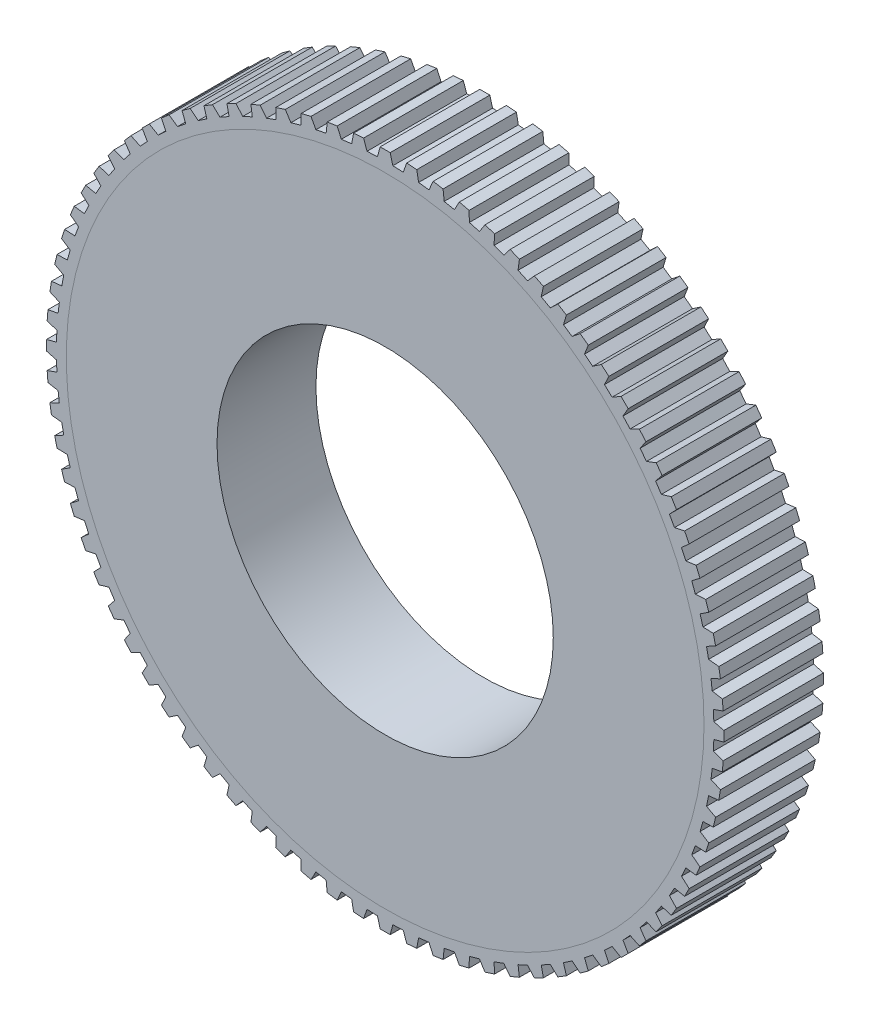
SolidWorks part; units mm, degrees
ref_plane "Front Plane" through (0, 0, 0) normal (0, 0, 1) x (1, 0, 0)
ref_plane "Top Plane" through (0, 0, 0) normal (0, 1, 0) x (1, 0, 0)
ref_plane "Right Plane" through (0, 0, 0) normal (1, 0, 0) x (0, 0, -1)
sketch "Sketch1" plane through (0, 0, 0) normal (0, 0, 1) x (1, 0, 0)
  circle A0 centre (0, 0) radius 8.5
  circle A1 centre (0, 0) radius 16.12
  dimension "D1" = 17
  dimension "D2" = 7.62
extrude "Boss-Extrude1" add sketch "Sketch1" along normal mid plane 5
sketch "Sketch2" plane through (0, 0, 0) normal (0, 0, 1) x (1, 0, 0)
  line L0 (0, 0) -> (0, 17.12) construction
  line L1 (-0.254, 17.12) -> (0.254, 17.12)
  line L2 (-0.254, 17.12) -> (-0.3892, 16.6154)
  line L3 (0.254, 17.12) -> (0.3892, 16.6154)
  line L4 (1.09, 17.0872) -> (0.9156, 16.5948)
  line L5 (1.09, 17.0872) -> (1.5964, 17.0473)
  line L6 (1.5964, 17.0473) -> (1.6916, 16.5337)
  line L7 (2.4273, 16.949) -> (2.2148, 16.4718)
  line L8 (2.4273, 16.949) -> (2.929, 16.8695)
  line L9 (2.929, 16.8695) -> (2.9836, 16.35)
  line L10 (3.7496, 16.7063) -> (3.5004, 16.2472)
  line L11 (3.7496, 16.7063) -> (4.2436, 16.5877)
  line L12 (4.2436, 16.5877) -> (4.2572, 16.0655)
  line L13 (5.0488, 16.3606) -> (4.7643, 15.9225)
  line L14 (5.0488, 16.3606) -> (5.5319, 16.2036)
  line L15 (5.5319, 16.2036) -> (5.5046, 15.682)
  line L16 (6.3169, 15.914) -> (5.9989, 15.4996)
  line L17 (6.3169, 15.914) -> (6.7862, 15.7196)
  line L18 (6.7862, 15.7196) -> (6.718, 15.2017)
  line L19 (7.546, 15.3693) -> (7.1965, 14.9812)
  line L20 (7.546, 15.3693) -> (7.9986, 15.1387)
  line L21 (7.9986, 15.1387) -> (7.89, 14.6278)
  line L22 (8.7286, 14.7299) -> (8.3497, 14.3703)
  line L23 (8.7286, 14.7299) -> (9.1617, 14.4645)
  line L24 (9.1617, 14.4645) -> (9.0134, 13.9636)
  line L25 (9.8574, 13.9997) -> (9.4514, 13.6709)
  line L26 (9.8574, 13.9997) -> (10.2684, 13.7011)
  line L27 (10.2684, 13.7011) -> (10.0812, 13.2134)
  line L28 (10.9254, 13.1831) -> (10.4949, 12.8872)
  line L29 (10.9254, 13.1831) -> (11.3117, 12.8532)
  line L30 (11.3117, 12.8532) -> (11.0868, 12.3817)
  line L31 (11.9261, 12.2853) -> (11.4737, 12.0241)
  line L32 (11.9261, 12.2853) -> (12.2853, 11.9261)
  line L33 (12.2853, 11.9261) -> (12.0241, 11.4737)
  line L34 (12.8532, 11.3117) -> (12.3817, 11.0868)
  line L35 (12.8532, 11.3117) -> (13.1831, 10.9254)
  line L36 (13.1831, 10.9254) -> (12.8872, 10.4949)
  line L37 (13.7011, 10.2684) -> (13.2134, 10.0812)
  line L38 (13.7011, 10.2684) -> (13.9997, 9.8574)
  line L39 (13.9997, 9.8574) -> (13.6709, 9.4514)
  line L40 (14.4645, 9.1617) -> (13.9636, 9.0134)
  line L41 (14.4645, 9.1617) -> (14.7299, 8.7286)
  line L42 (14.7299, 8.7286) -> (14.3703, 8.3497)
  line L43 (15.1387, 7.9986) -> (14.6278, 7.89)
  line L44 (15.1387, 7.9986) -> (15.3693, 7.546)
  line L45 (15.3693, 7.546) -> (14.9812, 7.1965)
  line L46 (15.7196, 6.7862) -> (15.2017, 6.718)
  line L47 (15.7196, 6.7862) -> (15.914, 6.3169)
  line L48 (15.914, 6.3169) -> (15.4996, 5.9989)
  line L49 (16.2036, 5.5319) -> (15.682, 5.5046)
  line L50 (16.2036, 5.5319) -> (16.3606, 5.0488)
  line L51 (16.3606, 5.0488) -> (15.9225, 4.7643)
  line L52 (16.5877, 4.2436) -> (16.0655, 4.2572)
  line L53 (16.5877, 4.2436) -> (16.7063, 3.7496)
  line L54 (16.7063, 3.7496) -> (16.2472, 3.5004)
  line L55 (16.8695, 2.929) -> (16.35, 2.9836)
  line L56 (16.8695, 2.929) -> (16.949, 2.4273)
  line L57 (16.949, 2.4273) -> (16.4718, 2.2148)
  line L58 (17.0473, 1.5964) -> (16.5337, 1.6916)
  line L59 (17.0473, 1.5964) -> (17.0872, 1.09)
  line L60 (17.0872, 1.09) -> (16.5948, 0.9156)
  line L61 (17.12, 0.254) -> (16.6154, 0.3892)
  line L62 (17.12, 0.254) -> (17.12, -0.254)
  line L63 (17.12, -0.254) -> (16.6154, -0.3892)
  line L64 (17.0872, -1.09) -> (16.5948, -0.9156)
  line L65 (17.0872, -1.09) -> (17.0473, -1.5964)
  line L66 (17.0473, -1.5964) -> (16.5337, -1.6916)
  line L67 (16.949, -2.4273) -> (16.4718, -2.2148)
  line L68 (16.949, -2.4273) -> (16.8695, -2.929)
  line L69 (16.8695, -2.929) -> (16.35, -2.9836)
  line L70 (16.7063, -3.7496) -> (16.2472, -3.5004)
  line L71 (16.7063, -3.7496) -> (16.5877, -4.2436)
  line L72 (16.5877, -4.2436) -> (16.0655, -4.2572)
  line L73 (16.3606, -5.0488) -> (15.9225, -4.7643)
  line L74 (16.3606, -5.0488) -> (16.2036, -5.5319)
  line L75 (16.2036, -5.5319) -> (15.682, -5.5046)
  line L76 (15.914, -6.3169) -> (15.4996, -5.9989)
  line L77 (15.914, -6.3169) -> (15.7196, -6.7862)
  line L78 (15.7196, -6.7862) -> (15.2017, -6.718)
  line L79 (15.3693, -7.546) -> (14.9812, -7.1965)
  line L80 (15.3693, -7.546) -> (15.1387, -7.9986)
  line L81 (15.1387, -7.9986) -> (14.6278, -7.89)
  line L82 (14.7299, -8.7286) -> (14.3703, -8.3497)
  line L83 (14.7299, -8.7286) -> (14.4645, -9.1617)
  line L84 (14.4645, -9.1617) -> (13.9636, -9.0134)
  line L85 (13.9997, -9.8574) -> (13.6709, -9.4514)
  line L86 (13.9997, -9.8574) -> (13.7011, -10.2684)
  line L87 (13.7011, -10.2684) -> (13.2134, -10.0812)
  line L88 (13.1831, -10.9254) -> (12.8872, -10.4949)
  line L89 (13.1831, -10.9254) -> (12.8532, -11.3117)
  line L90 (12.8532, -11.3117) -> (12.3817, -11.0868)
  line L91 (12.2853, -11.9261) -> (12.0241, -11.4737)
  line L92 (12.2853, -11.9261) -> (11.9261, -12.2853)
  line L93 (11.9261, -12.2853) -> (11.4737, -12.0241)
  line L94 (11.3117, -12.8532) -> (11.0868, -12.3817)
  line L95 (11.3117, -12.8532) -> (10.9254, -13.1831)
  line L96 (10.9254, -13.1831) -> (10.4949, -12.8872)
  line L97 (10.2684, -13.7011) -> (10.0812, -13.2134)
  line L98 (10.2684, -13.7011) -> (9.8574, -13.9997)
  line L99 (9.8574, -13.9997) -> (9.4514, -13.6709)
  line L100 (9.1617, -14.4645) -> (9.0134, -13.9636)
  line L101 (9.1617, -14.4645) -> (8.7286, -14.7299)
  line L102 (8.7286, -14.7299) -> (8.3497, -14.3703)
  line L103 (7.9986, -15.1387) -> (7.89, -14.6278)
  line L104 (7.9986, -15.1387) -> (7.546, -15.3693)
  line L105 (7.546, -15.3693) -> (7.1965, -14.9812)
  line L106 (6.7862, -15.7196) -> (6.718, -15.2017)
  line L107 (6.7862, -15.7196) -> (6.3169, -15.914)
  line L108 (6.3169, -15.914) -> (5.9989, -15.4996)
  line L109 (5.5319, -16.2036) -> (5.5046, -15.682)
  line L110 (5.5319, -16.2036) -> (5.0488, -16.3606)
  line L111 (5.0488, -16.3606) -> (4.7643, -15.9225)
  line L112 (4.2436, -16.5877) -> (4.2572, -16.0655)
  line L113 (4.2436, -16.5877) -> (3.7496, -16.7063)
  line L114 (3.7496, -16.7063) -> (3.5004, -16.2472)
  line L115 (2.929, -16.8695) -> (2.9836, -16.35)
  line L116 (2.929, -16.8695) -> (2.4273, -16.949)
  line L117 (2.4273, -16.949) -> (2.2148, -16.4718)
  line L118 (1.5964, -17.0473) -> (1.6916, -16.5337)
  line L119 (1.5964, -17.0473) -> (1.09, -17.0872)
  line L120 (1.09, -17.0872) -> (0.9156, -16.5948)
  line L121 (0.254, -17.12) -> (0.3892, -16.6154)
  line L122 (0.254, -17.12) -> (-0.254, -17.12)
  line L123 (-0.254, -17.12) -> (-0.3892, -16.6154)
  line L124 (-1.09, -17.0872) -> (-0.9156, -16.5948)
  line L125 (-1.09, -17.0872) -> (-1.5964, -17.0473)
  line L126 (-1.5964, -17.0473) -> (-1.6916, -16.5337)
  line L127 (-2.4273, -16.949) -> (-2.2148, -16.4718)
  line L128 (-2.4273, -16.949) -> (-2.929, -16.8695)
  line L129 (-2.929, -16.8695) -> (-2.9836, -16.35)
  line L130 (-3.7496, -16.7063) -> (-3.5004, -16.2472)
  line L131 (-3.7496, -16.7063) -> (-4.2436, -16.5877)
  line L132 (-4.2436, -16.5877) -> (-4.2572, -16.0655)
  line L133 (-5.0488, -16.3606) -> (-4.7643, -15.9225)
  line L134 (-5.0488, -16.3606) -> (-5.5319, -16.2036)
  line L135 (-5.5319, -16.2036) -> (-5.5046, -15.682)
  line L136 (-6.3169, -15.914) -> (-5.9989, -15.4996)
  line L137 (-6.3169, -15.914) -> (-6.7862, -15.7196)
  line L138 (-6.7862, -15.7196) -> (-6.718, -15.2017)
  line L139 (-7.546, -15.3693) -> (-7.1965, -14.9812)
  line L140 (-7.546, -15.3693) -> (-7.9986, -15.1387)
  line L141 (-7.9986, -15.1387) -> (-7.89, -14.6278)
  line L142 (-8.7286, -14.7299) -> (-8.3497, -14.3703)
  line L143 (-8.7286, -14.7299) -> (-9.1617, -14.4645)
  line L144 (-9.1617, -14.4645) -> (-9.0134, -13.9636)
  line L145 (-9.8574, -13.9997) -> (-9.4514, -13.6709)
  line L146 (-9.8574, -13.9997) -> (-10.2684, -13.7011)
  line L147 (-10.2684, -13.7011) -> (-10.0812, -13.2134)
  line L148 (-10.9254, -13.1831) -> (-10.4949, -12.8872)
  line L149 (-10.9254, -13.1831) -> (-11.3117, -12.8532)
  line L150 (-11.3117, -12.8532) -> (-11.0868, -12.3817)
  line L151 (-11.9261, -12.2853) -> (-11.4737, -12.0241)
  line L152 (-11.9261, -12.2853) -> (-12.2853, -11.9261)
  line L153 (-12.2853, -11.9261) -> (-12.0241, -11.4737)
  line L154 (-12.8532, -11.3117) -> (-12.3817, -11.0868)
  line L155 (-12.8532, -11.3117) -> (-13.1831, -10.9254)
  line L156 (-13.1831, -10.9254) -> (-12.8872, -10.4949)
  line L157 (-13.7011, -10.2684) -> (-13.2134, -10.0812)
  line L158 (-13.7011, -10.2684) -> (-13.9997, -9.8574)
  line L159 (-13.9997, -9.8574) -> (-13.6709, -9.4514)
  line L160 (-14.4645, -9.1617) -> (-13.9636, -9.0134)
  line L161 (-14.4645, -9.1617) -> (-14.7299, -8.7286)
  line L162 (-14.7299, -8.7286) -> (-14.3703, -8.3497)
  line L163 (-15.1387, -7.9986) -> (-14.6278, -7.89)
  line L164 (-15.1387, -7.9986) -> (-15.3693, -7.546)
  line L165 (-15.3693, -7.546) -> (-14.9812, -7.1965)
  line L166 (-15.7196, -6.7862) -> (-15.2017, -6.718)
  line L167 (-15.7196, -6.7862) -> (-15.914, -6.3169)
  line L168 (-15.914, -6.3169) -> (-15.4996, -5.9989)
  line L169 (-16.2036, -5.5319) -> (-15.682, -5.5046)
  line L170 (-16.2036, -5.5319) -> (-16.3606, -5.0488)
  line L171 (-16.3606, -5.0488) -> (-15.9225, -4.7643)
  line L172 (-16.5877, -4.2436) -> (-16.0655, -4.2572)
  line L173 (-16.5877, -4.2436) -> (-16.7063, -3.7496)
  line L174 (-16.7063, -3.7496) -> (-16.2472, -3.5004)
  line L175 (-16.8695, -2.929) -> (-16.35, -2.9836)
  line L176 (-16.8695, -2.929) -> (-16.949, -2.4273)
  line L177 (-16.949, -2.4273) -> (-16.4718, -2.2148)
  line L178 (-17.0473, -1.5964) -> (-16.5337, -1.6916)
  line L179 (-17.0473, -1.5964) -> (-17.0872, -1.09)
  line L180 (-17.0872, -1.09) -> (-16.5948, -0.9156)
  line L181 (-17.12, -0.254) -> (-16.6154, -0.3892)
  line L182 (-17.12, -0.254) -> (-17.12, 0.254)
  line L183 (-17.12, 0.254) -> (-16.6154, 0.3892)
  line L184 (-17.0872, 1.09) -> (-16.5948, 0.9156)
  line L185 (-17.0872, 1.09) -> (-17.0473, 1.5964)
  line L186 (-17.0473, 1.5964) -> (-16.5337, 1.6916)
  line L187 (-16.949, 2.4273) -> (-16.4718, 2.2148)
  line L188 (-16.949, 2.4273) -> (-16.8695, 2.929)
  line L189 (-16.8695, 2.929) -> (-16.35, 2.9836)
  line L190 (-16.7063, 3.7496) -> (-16.2472, 3.5004)
  line L191 (-16.7063, 3.7496) -> (-16.5877, 4.2436)
  line L192 (-16.5877, 4.2436) -> (-16.0655, 4.2572)
  line L193 (-16.3606, 5.0488) -> (-15.9225, 4.7643)
  line L194 (-16.3606, 5.0488) -> (-16.2036, 5.5319)
  line L195 (-16.2036, 5.5319) -> (-15.682, 5.5046)
  line L196 (-15.914, 6.3169) -> (-15.4996, 5.9989)
  line L197 (-15.914, 6.3169) -> (-15.7196, 6.7862)
  line L198 (-15.7196, 6.7862) -> (-15.2017, 6.718)
  line L199 (-15.3693, 7.546) -> (-14.9812, 7.1965)
  line L200 (-15.3693, 7.546) -> (-15.1387, 7.9986)
  line L201 (-15.1387, 7.9986) -> (-14.6278, 7.89)
  line L202 (-14.7299, 8.7286) -> (-14.3703, 8.3497)
  line L203 (-14.7299, 8.7286) -> (-14.4645, 9.1617)
  line L204 (-14.4645, 9.1617) -> (-13.9636, 9.0134)
  line L205 (-13.9997, 9.8574) -> (-13.6709, 9.4514)
  line L206 (-13.9997, 9.8574) -> (-13.7011, 10.2684)
  line L207 (-13.7011, 10.2684) -> (-13.2134, 10.0812)
  line L208 (-13.1831, 10.9254) -> (-12.8872, 10.4949)
  line L209 (-13.1831, 10.9254) -> (-12.8532, 11.3117)
  line L210 (-12.8532, 11.3117) -> (-12.3817, 11.0868)
  line L211 (-12.2853, 11.9261) -> (-12.0241, 11.4737)
  line L212 (-12.2853, 11.9261) -> (-11.9261, 12.2853)
  line L213 (-11.9261, 12.2853) -> (-11.4737, 12.0241)
  line L214 (-11.3117, 12.8532) -> (-11.0868, 12.3817)
  line L215 (-11.3117, 12.8532) -> (-10.9254, 13.1831)
  line L216 (-10.9254, 13.1831) -> (-10.4949, 12.8872)
  line L217 (-10.2684, 13.7011) -> (-10.0812, 13.2134)
  line L218 (-10.2684, 13.7011) -> (-9.8574, 13.9997)
  line L219 (-9.8574, 13.9997) -> (-9.4514, 13.6709)
  line L220 (-9.1617, 14.4645) -> (-9.0134, 13.9636)
  line L221 (-9.1617, 14.4645) -> (-8.7286, 14.7299)
  line L222 (-8.7286, 14.7299) -> (-8.3497, 14.3703)
  line L223 (-7.9986, 15.1387) -> (-7.89, 14.6278)
  line L224 (-7.9986, 15.1387) -> (-7.546, 15.3693)
  line L225 (-7.546, 15.3693) -> (-7.1965, 14.9812)
  line L226 (-6.7862, 15.7196) -> (-6.718, 15.2017)
  line L227 (-6.7862, 15.7196) -> (-6.3169, 15.914)
  line L228 (-6.3169, 15.914) -> (-5.9989, 15.4996)
  line L229 (-5.5319, 16.2036) -> (-5.5046, 15.682)
  line L230 (-5.5319, 16.2036) -> (-5.0488, 16.3606)
  line L231 (-5.0488, 16.3606) -> (-4.7643, 15.9225)
  line L232 (-4.2436, 16.5877) -> (-4.2572, 16.0655)
  line L233 (-4.2436, 16.5877) -> (-3.7496, 16.7063)
  line L234 (-3.7496, 16.7063) -> (-3.5004, 16.2472)
  line L235 (-2.929, 16.8695) -> (-2.9836, 16.35)
  line L236 (-2.929, 16.8695) -> (-2.4273, 16.949)
  line L237 (-2.4273, 16.949) -> (-2.2148, 16.4718)
  line L238 (-1.5964, 17.0473) -> (-1.6916, 16.5337)
  line L239 (-1.5964, 17.0473) -> (-1.09, 17.0872)
  line L240 (-1.09, 17.0872) -> (-0.9156, 16.5948)
  line L241 (0.3892, 16.6154) -> (0.9156, 16.5948)
  line L242 (1.6916, 16.5337) -> (2.2148, 16.4718)
  line L243 (2.9836, 16.35) -> (3.5004, 16.2472)
  line L244 (4.2572, 16.0655) -> (4.7643, 15.9225)
  line L245 (5.5046, 15.682) -> (5.9989, 15.4996)
  line L246 (6.718, 15.2017) -> (7.1965, 14.9812)
  line L247 (7.89, 14.6278) -> (8.3497, 14.3703)
  line L248 (9.0134, 13.9636) -> (9.4514, 13.6709)
  line L249 (10.0812, 13.2134) -> (10.4949, 12.8872)
  line L250 (11.0868, 12.3817) -> (11.4737, 12.0241)
  line L251 (12.0241, 11.4737) -> (12.3817, 11.0868)
  line L252 (12.8872, 10.4949) -> (13.2134, 10.0812)
  line L253 (13.6709, 9.4514) -> (13.9636, 9.0134)
  line L254 (14.3703, 8.3497) -> (14.6278, 7.89)
  line L255 (14.9812, 7.1965) -> (15.2017, 6.718)
  line L256 (15.4996, 5.9989) -> (15.682, 5.5046)
  line L257 (15.9225, 4.7643) -> (16.0655, 4.2572)
  line L258 (16.2472, 3.5004) -> (16.35, 2.9836)
  line L259 (16.4718, 2.2148) -> (16.5337, 1.6916)
  line L260 (16.5948, 0.9156) -> (16.6154, 0.3892)
  line L261 (16.6154, -0.3892) -> (16.5948, -0.9156)
  line L262 (16.5337, -1.6916) -> (16.4718, -2.2148)
  line L263 (16.35, -2.9836) -> (16.2472, -3.5004)
  line L264 (16.0655, -4.2572) -> (15.9225, -4.7643)
  line L265 (15.682, -5.5046) -> (15.4996, -5.9989)
  line L266 (15.2017, -6.718) -> (14.9812, -7.1965)
  line L267 (14.6278, -7.89) -> (14.3703, -8.3497)
  line L268 (13.9636, -9.0134) -> (13.6709, -9.4514)
  line L269 (13.2134, -10.0812) -> (12.8872, -10.4949)
  line L270 (12.3817, -11.0868) -> (12.0241, -11.4737)
  line L271 (11.4737, -12.0241) -> (11.0868, -12.3817)
  line L272 (10.4949, -12.8872) -> (10.0812, -13.2134)
  line L273 (9.4514, -13.6709) -> (9.0134, -13.9636)
  line L274 (8.3497, -14.3703) -> (7.89, -14.6278)
  line L275 (7.1965, -14.9812) -> (6.718, -15.2017)
  line L276 (5.9989, -15.4996) -> (5.5046, -15.682)
  line L277 (4.7643, -15.9225) -> (4.2572, -16.0655)
  line L278 (3.5004, -16.2472) -> (2.9836, -16.35)
  line L279 (2.2148, -16.4718) -> (1.6916, -16.5337)
  line L280 (0.9156, -16.5948) -> (0.3892, -16.6154)
  line L281 (-0.3892, -16.6154) -> (-0.9156, -16.5948)
  line L282 (-1.6916, -16.5337) -> (-2.2148, -16.4718)
  line L283 (-2.9836, -16.35) -> (-3.5004, -16.2472)
  line L284 (-4.2572, -16.0655) -> (-4.7643, -15.9225)
  line L285 (-5.5046, -15.682) -> (-5.9989, -15.4996)
  line L286 (-6.718, -15.2017) -> (-7.1965, -14.9812)
  line L287 (-7.89, -14.6278) -> (-8.3497, -14.3703)
  line L288 (-9.0134, -13.9636) -> (-9.4514, -13.6709)
  line L289 (-10.0812, -13.2134) -> (-10.4949, -12.8872)
  line L290 (-11.0868, -12.3817) -> (-11.4737, -12.0241)
  line L291 (-12.0241, -11.4737) -> (-12.3817, -11.0868)
  line L292 (-12.8872, -10.4949) -> (-13.2134, -10.0812)
  line L293 (-13.6709, -9.4514) -> (-13.9636, -9.0134)
  line L294 (-14.3703, -8.3497) -> (-14.6278, -7.89)
  line L295 (-14.9812, -7.1965) -> (-15.2017, -6.718)
  line L296 (-15.4996, -5.9989) -> (-15.682, -5.5046)
  line L297 (-15.9225, -4.7643) -> (-16.0655, -4.2572)
  line L298 (-16.2472, -3.5004) -> (-16.35, -2.9836)
  line L299 (-16.4718, -2.2148) -> (-16.5337, -1.6916)
  line L300 (-16.5948, -0.9156) -> (-16.6154, -0.3892)
  line L301 (-16.6154, 0.3892) -> (-16.5948, 0.9156)
  line L302 (-16.5337, 1.6916) -> (-16.4718, 2.2148)
  line L303 (-16.35, 2.9836) -> (-16.2472, 3.5004)
  line L304 (-16.0655, 4.2572) -> (-15.9225, 4.7643)
  line L305 (-15.682, 5.5046) -> (-15.4996, 5.9989)
  line L306 (-15.2017, 6.718) -> (-14.9812, 7.1965)
  line L307 (-14.6278, 7.89) -> (-14.3703, 8.3497)
  line L308 (-13.9636, 9.0134) -> (-13.6709, 9.4514)
  line L309 (-13.2134, 10.0812) -> (-12.8872, 10.4949)
  line L310 (-12.3817, 11.0868) -> (-12.0241, 11.4737)
  line L311 (-11.4737, 12.0241) -> (-11.0868, 12.3817)
  line L312 (-10.4949, 12.8872) -> (-10.0812, 13.2134)
  line L313 (-9.4514, 13.6709) -> (-9.0134, 13.9636)
  line L314 (-8.3497, 14.3703) -> (-7.89, 14.6278)
  line L315 (-7.1965, 14.9812) -> (-6.718, 15.2017)
  line L316 (-5.9989, 15.4996) -> (-5.5046, 15.682)
  line L317 (-4.7643, 15.9225) -> (-4.2572, 16.0655)
  line L318 (-3.5004, 16.2472) -> (-2.9836, 16.35)
  line L319 (-2.2148, 16.4718) -> (-1.6916, 16.5337)
  line L320 (-0.9156, 16.5948) -> (-0.3892, 16.6154)
  circle A0 centre (0, 0) radius 16.12 construction
  circle A1 centre (0, 0) radius 16.12
  circle A2 centre (0, 0) radius 17.12 construction
  circle A3 centre (0, 0) radius 16.62 construction
  point P11 (0, 17.12)
  point P332 (0, 0)
  point P491 (0, 0)
  dimension "D3" = 0.508
  dimension "D4" = 15
  dimension "D5" = 15
  dimension "D1" = 1
  dimension "D2" = 0.5
  dimension "D6" = 80
  dimension "D7" = 80
extrude "Boss-Extrude2" add sketch "Sketch2" along normal up to surface (2.5 mm away) and the other way blind 2.54 separate body up to face at (16.12, 0, 2.5)
